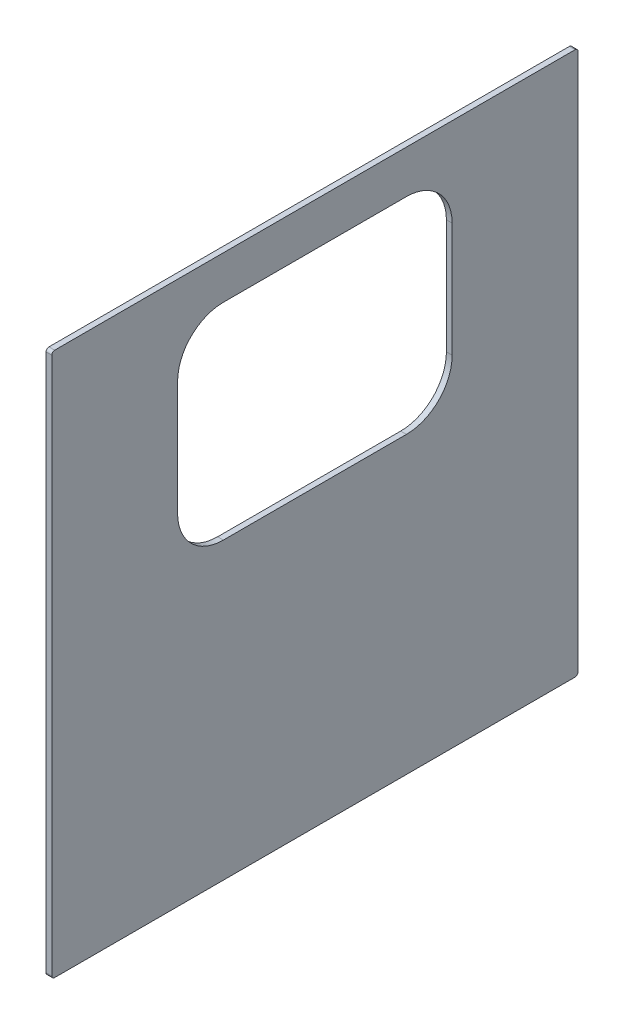
SolidWorks part; units mm, degrees
material "PE High Density"
ref_plane "Front Plane" through (0, 0, 0) normal (0, 0, 1) x (1, 0, 0)
ref_plane "Top Plane" through (0, 0, 0) normal (0, 1, 0) x (1, 0, 0)
ref_plane "Right Plane" through (0, 0, 0) normal (1, 0, 0) x (0, 0, -1)
sketch "Sketch1" plane through (0, 0, 0) normal (1, 0, 0) x (0, 0, -1)
  line L0 (6.35, 0) -> (1162.05, 0)
  line L1 (0, 6.35) -> (0, 1200.15)
  line L2 (1168.4, 6.35) -> (1168.4, 1200.15)
  line L3 (6.35, 1206.5) -> (1162.05, 1206.5)
  line L4 (381, 1111.25) -> (787.4, 1111.25)
  line L5 (279.4, 1009.65) -> (279.4, 755.65)
  line L6 (889, 1009.65) -> (889, 755.65)
  line L7 (381, 654.05) -> (787.4, 654.05)
  line L8 (279.4, 755.65) -> (0, 755.65) construction
  line L9 (889, 755.65) -> (1168.4, 755.65) construction
  arc A0 (0, 6.35) -> (6.35, 0) centre (6.35, 6.35) ccw
  arc A1 (1162.05, 0) -> (1168.4, 6.35) centre (1162.05, 6.35) ccw
  arc A2 (1168.4, 1200.15) -> (1162.05, 1206.5) centre (1162.05, 1200.15) ccw
  arc A3 (6.35, 1206.5) -> (0, 1200.15) centre (6.35, 1200.15) ccw
  arc A4 (279.4, 755.65) -> (381, 654.05) centre (381, 755.65) ccw
  arc A5 (889, 755.65) -> (787.4, 654.05) centre (787.4, 755.65) cw
  arc A6 (787.4, 1111.25) -> (889, 1009.65) centre (787.4, 1009.65) cw
  arc A7 (279.4, 1009.65) -> (381, 1111.25) centre (381, 1009.65) cw
  point P11 (0, 0)
  point P14 (1168.4, 0)
  point P17 (1168.4, 1206.5)
  point P20 (0, 1206.5)
  point P23 (279.4, 654.05)
  point P28 (889, 1111.25)
  point P31 (279.4, 1111.25)
  dimension "D7" = 6.35
  dimension "D8" = 101.6
  dimension "D1" = 1168.4
  dimension "D2" = 609.6
  dimension "D4" = 1206.5
  dimension "D5" = 654.05
  dimension "D6" = 457.2
extrude "Boss-Extrude1" add sketch "Sketch1" along normal blind 12.7
